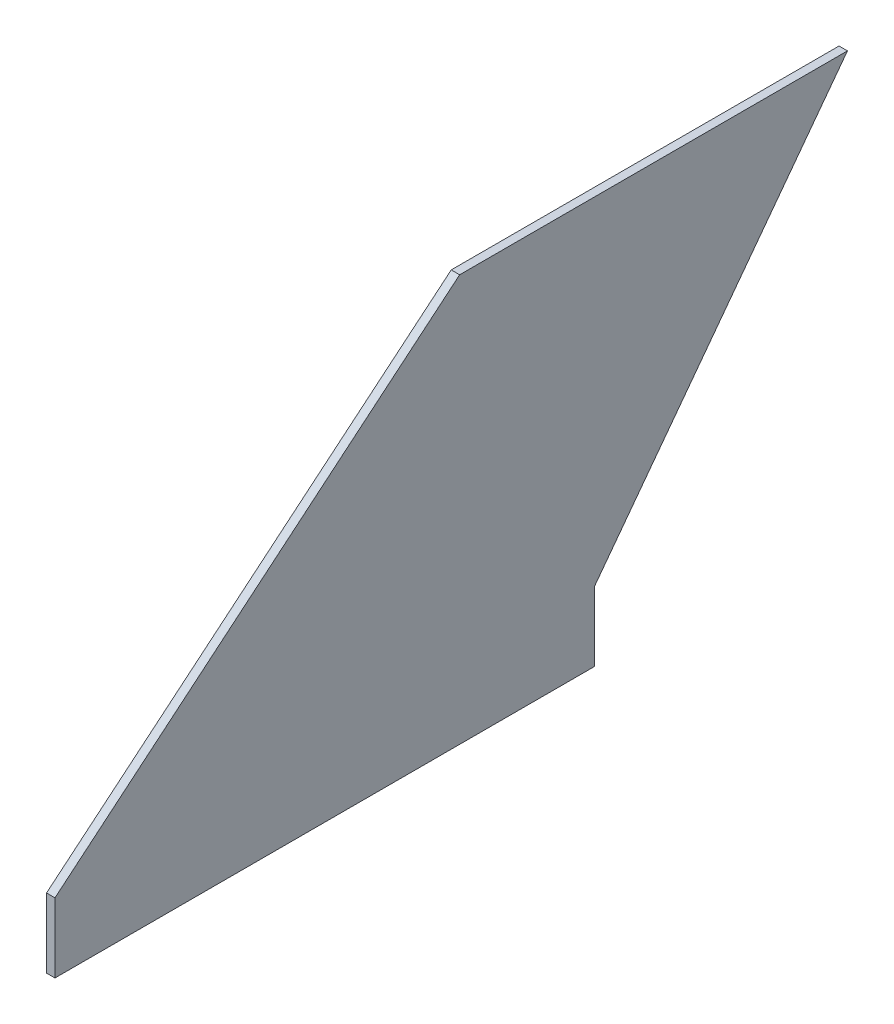
SolidWorks part; units mm, degrees
ref_plane "Front Plane" through (0, 0, 0) normal (0, 0, 1) x (1, 0, 0)
ref_plane "Top Plane" through (0, 0, 0) normal (0, 1, 0) x (1, 0, 0)
ref_plane "Right Plane" through (0, 0, 0) normal (1, 0, 0) x (0, 0, -1)
sketch "Sketch2" plane through (0, 0, 0) normal (1, 0, 0) x (0, 0, -1)
  line L0 (0, 0) -> (152.4, 127)
  line L1 (0, -26.1493) -> (203.2, -26.1493)
  line L2 (0, -26.1493) -> (0, 0)
  line L3 (0, 0) -> (203.2, 0) construction
  line L4 (203.2, -26.1493) -> (203.2, 0)
  line L5 (0, -26.1493) -> (203.2, 0) construction
  line L6 (0, 0) -> (203.2, -26.1493) construction
  line L7 (152.4, 127) -> (298.45, 127)
  line L8 (298.45, 127) -> (203.2, 0)
  point P0 (101.6, -13.0746)
  dimension "D1" = 152.4
  dimension "D2" = 127
  dimension "D3" = 298.45
  dimension "D4" = 203.2
  dimension "D5" = 26.1493
extrude "Boss-Extrude1" add sketch "Sketch2" along normal blind 3.175
equation "\"AIRFRAME_OD\"= 5.15in"
equation "\"AIRFRAME_ID\"= 5.00in"
equation "\"FLAT_T\"= 0.125in"
equation "\"COUPLER_OD\"= 4.998in"
equation "\"COUPLER_ID\"= 4.88in"
equation "\"NOSE_EXP_L\"= 27in"
equation "\"NOSE_SHOULDER_L\"= 5in"
equation "\"MAIN_L\"= 30in"
equation "\"RECO_COUP_L\"= 10in"
equation "\"RECO_SWITCH_L\"= 2in"
equation "\"RECO_ROD_X\"= 3.5in"
equation "\"DROGUE_L\"= 20in"
equation "\"ATS_FORE_COUP_L\"= 5.5in"
equation "\"ATS_AFT_COUP_L\"= 4.5in"
equation "\"ATS_ROD_X\"= 3.75in"
equation "\"LOWER_L\"= 30in"
equation "\"FIN_ROOT\"= 8in"
equation "\"FIN_X\"= 0.75in"
equation "\"FIN_N\"= 4"
equation "\"MOTOR_OD\"= 3.091in"
equation "\"MOTOR_ID\"= 3.00in"
equation "\"MOTOR_L\"= 14in"
equation "\"CR_AFT_X\"= 0.5in"
equation "\"CR_FORE_X\"= 9.25in"
equation "\"D1@Boss-Extrude1\"=\"FLAT_T\""
equation "\"D4@Sketch2\"=\"FIN_ROOT\""
equation "\"D5@Sketch2\"=(\"AIRFRAME_OD\"-\"MOTOR_OD\")*0.5"
equation "\"MOTOR_LOWER_X\"= 2in"
